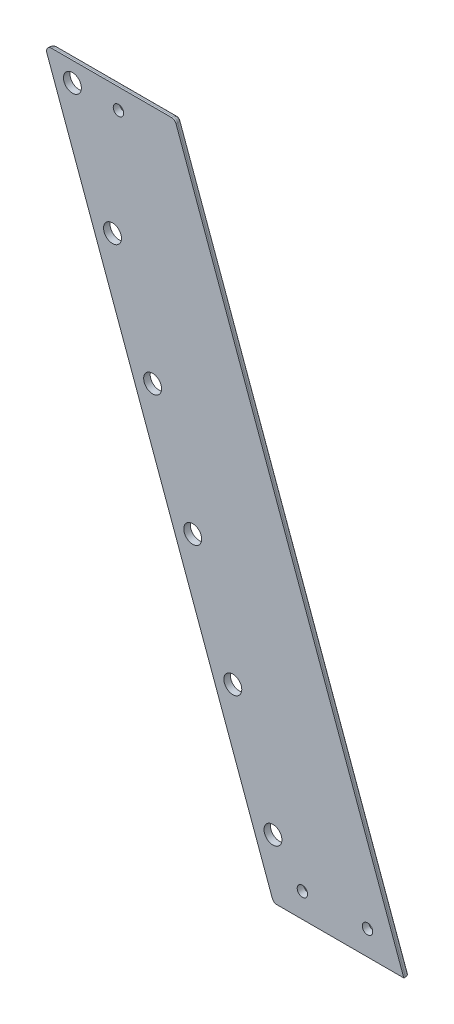
SolidWorks part; units mm, degrees
ref_plane "Front Plane" through (0, 0, 0) normal (0, 0, 1) x (1, 0, 0)
ref_plane "Top Plane" through (0, 0, 0) normal (0, 1, 0) x (1, 0, 0)
ref_plane "Right Plane" through (0, 0, 0) normal (1, 0, 0) x (0, 0, -1)
sketch "Sketch3" plane through (0, 0, 0) normal (0, 0, 1) x (1, 0, 0)
  line L1 (-127.0377, 609.9404) -> (92.9623, 609.9404)
  line L2 (-127.0377, 609.9404) -> (-127.0377, 389.9404)
  line L3 (-127.0377, 389.9404) -> (92.9623, 389.9404)
  line L4 (92.9623, 609.9404) -> (92.9623, 389.9404)
  dimension "D1" = 220
  dimension "D2" = 220
sketch "Sketch1" plane through (0, 0, 0) normal (0, 0, 1) x (1, 0, 0)
  line L0 (5, 40.95) -> (25, 40.95)
  line L1 (0, 0) -> (30, 0)
  line L2 (0, 0) -> (0, 34.5)
  line L3 (0, 34.5) -> (30, 34.5)
  line L4 (30, 0) -> (30, 34.5)
  line L5 (0, 0) -> (30, 0)
  line L6 (0, 0) -> (0, -4)
  line L7 (0, -4) -> (30, -4)
  line L8 (30, 0) -> (30, -4)
  line L9 (0, 34.5) -> (30, 34.5)
  line L10 (0, 34.5) -> (0, 44.5)
  line L11 (0, 44.5) -> (30, 44.5)
  line L12 (30, 34.5) -> (30, 44.5)
  line L14 (8.2332, 40.95) -> (6.6166, 43.75)
  line L15 (6.6166, 43.75) -> (3.3834, 43.75)
  line L16 (3.3834, 43.75) -> (1.7668, 40.95)
  line L17 (1.7668, 40.95) -> (3.3834, 38.15)
  line L18 (3.3834, 38.15) -> (6.6166, 38.15)
  line L19 (6.6166, 38.15) -> (8.2332, 40.95)
  line L20 (21.7668, 40.95) -> (23.3834, 38.15)
  line L21 (23.3834, 38.15) -> (26.6166, 38.15)
  line L22 (26.6166, 38.15) -> (28.2332, 40.95)
  line L23 (28.2332, 40.95) -> (26.6166, 43.75)
  line L24 (26.6166, 43.75) -> (23.3834, 43.75)
  line L25 (23.3834, 43.75) -> (21.7668, 40.95)
  circle A0 centre (15, 8) radius 6.5
  circle A1 centre (5, 40.95) radius 1.55
  circle A2 centre (25, 40.95) radius 1.55
  circle A3 centre (5, 40.95) radius 2.8 construction
  circle A4 centre (25, 40.95) radius 2.8 construction
  point P10 (15, 0)
  point P16 (5, 42.5)
  point P17 (5, 39.4)
  point P18 (15, 40.95)
  point P19 (15, 34.5)
  dimension "D4" = 13
  dimension "D7" = 3.1
  dimension "D10" = 5.6
  dimension "D1" = 30
  dimension "D2" = 34.5
  dimension "D3" = 4
  dimension "D5" = 8
  dimension "D6" = 20
  dimension "D8" = 4.9
  dimension "D9" = 2
sketch "Sketch2" plane through (0, 0, 0) normal (0, 0, 1) x (1, 0, 0)
  line L0 (0, 34.5) -> (-53.8676, 182.5)
  line L1 (-53.8676, 182.5) -> (-53.8676, 34.5)
  line L2 (-53.8676, 34.5) -> (0, 34.5)
  line L3 (30, 44.5) -> (-82.8834, 354.6447)
  line L4 (-82.8834, 354.6447) -> (-119.7157, 354.6447)
  line L5 (-119.7157, 354.6447) -> (-3.1925, 34.5)
  line L6 (-53.8676, 182.5) -> (-115.4312, 351.6447)
  line L7 (-55.9682, 179.5) -> (-19.136, 179.5)
  line L8 (-50.5087, 164.5) -> (-13.6764, 164.5)
  line L9 (-44.8223, 172) -> (-24.8223, 172)
  line L10 (-24.8223, 168.7668) -> (-22.0223, 170.3834)
  line L11 (-22.0223, 170.3834) -> (-22.0223, 173.6166)
  line L12 (-22.0223, 173.6166) -> (-24.8223, 175.2332)
  line L13 (-24.8223, 175.2332) -> (-27.6223, 173.6166)
  line L14 (-27.6223, 173.6166) -> (-27.6223, 170.3834)
  line L15 (-27.6223, 170.3834) -> (-24.8223, 168.7668)
  line L16 (-44.8223, 168.7668) -> (-42.0223, 170.3834)
  line L17 (-42.0223, 170.3834) -> (-42.0223, 173.6166)
  line L18 (-42.0223, 173.6166) -> (-44.8223, 175.2332)
  line L19 (-44.8223, 175.2332) -> (-47.6223, 173.6166)
  line L20 (-47.6223, 173.6166) -> (-47.6223, 170.3834)
  line L21 (-47.6223, 170.3834) -> (-44.8223, 168.7668)
  line L22 (-37.5521, 179.5) -> (-32.0925, 164.5)
  line L23 (-22.3285, 179.5) -> (-16.869, 164.5)
  line L24 (-52.7757, 179.5) -> (-47.3161, 164.5)
  line L25 (-44.1637, 179.5) -> (4.9723, 44.5)
  line L26 (0, 44.5) -> (30, 44.5) construction
  line L27 (-30.9405, 179.5) -> (18.1955, 44.5)
  line L28 (4.9723, 44.5) -> (18.1955, 44.5)
  line L29 (-44.1637, 179.5) -> (-30.9405, 179.5)
  line L30 (18.1955, 44.5) -> (30, 44.5)
  line L31 (4.9723, 44.5) -> (0, 44.5)
  line L32 (0, 44.5) -> (0, 34.5)
  line L33 (-3.1925, 34.5) -> (0, 25.7286)
  line L34 (0, 0) -> (0, 34.5) construction
  line L35 (0, 25.7286) -> (0, 34.5)
  line L36 (-50.5087, 164.5) -> (-53.7012, 164.5)
  line L37 (-53.7012, 164.5) -> (-124.0001, 357.6447)
  line L41 (-82.8834, 354.6447) -> (-83.9753, 357.6447)
  line L42 (-83.9753, 357.6447) -> (-124.0001, 357.6447)
  line L43 (-22.3285, 179.5) -> (-86.076, 354.6447)
  line L44 (-101.2995, 354.6447) -> (-104.0995, 353.0281)
  line L45 (-104.0995, 353.0281) -> (-104.0995, 349.7949)
  line L46 (-104.0995, 349.7949) -> (-101.2995, 348.1783)
  line L47 (-101.2995, 348.1783) -> (-98.4995, 349.7949)
  line L48 (-98.4995, 349.7949) -> (-98.4995, 353.0281)
  line L49 (-98.4995, 353.0281) -> (-101.2995, 354.6447)
  line L50 (-98.4995, 353.0281) -> (-104.0995, 353.0281)
  line L51 (-98.4995, 353.0281) -> (-98.4995, 357.6447)
  line L52 (-98.4995, 357.6447) -> (-104.0995, 357.6447)
  line L53 (-104.0995, 353.0281) -> (-104.0995, 357.6447)
  circle A0 centre (-53.8676, 182.5) radius 2.5
  circle A1 centre (-66.1803, 216.3289) radius 2.5
  circle A2 centre (-78.493, 250.1579) radius 2.5
  circle A3 centre (-90.8058, 283.9868) radius 2.5
  circle A4 centre (-103.1185, 317.8157) radius 2.5
  circle A5 centre (-115.4312, 351.6447) radius 2.5
  circle A6 centre (-115.4312, 351.6447) radius 3
  circle A7 centre (-53.8676, 182.5) radius 3
  circle A8 centre (-24.8223, 172) radius 2.8 construction
  circle A9 centre (-44.8223, 172) radius 2.8 construction
  circle A10 centre (-44.8223, 172) radius 1.6
  circle A11 centre (-24.8223, 172) radius 1.6
  circle A12 centre (-101.2995, 351.4115) radius 2.8 construction
  circle A13 centre (-101.2995, 351.4115) radius 1.6
  circle A14 centre (-53.8676, 182.5) radius 2.75
  circle A15 centre (-66.1803, 216.3289) radius 2.75
  circle A16 centre (-78.493, 250.1579) radius 2.75
  circle A17 centre (-90.8058, 283.9868) radius 2.75
  circle A18 centre (-115.4312, 351.6447) radius 2.75
  circle A19 centre (-103.1185, 317.8157) radius 2.75
  point P44 (-34.8223, 172)
  point P45 (-34.8223, 172)
  point P78 (-101.2995, 354.6447)
  dimension "D3" = 5
  dimension "D5" = 6
  dimension "D8" = 5.6
  dimension "D10" = 3.2
  dimension "D16" = 5.6
  dimension "D18" = 3.2
  dimension "D17" = 5.5
  dimension "D1" = 148
  dimension "D2" = 70
  dimension "D6" = 180
  dimension "D7" = 15
  dimension "D9" = 20
  dimension "D11" = 3
  dimension "D12" = 3
  dimension "D13" = 12.4258
  dimension "D14" = 3
  dimension "D15" = 3
  dimension "D4" = 6
extrude "Boss-Extrude1" add sketch "Sketch2" along normal blind 2
fillet "Fillet1" radius 1.5 6 edges at (-83.9753, 357.6447, 1) (-124.0001, 357.6447, 1) (-53.7012, 164.5, 1) (-88.8507, 261.0723, 0) (-103.9877, 357.6447, 0) (-48.8259, 261.0723, 0)
